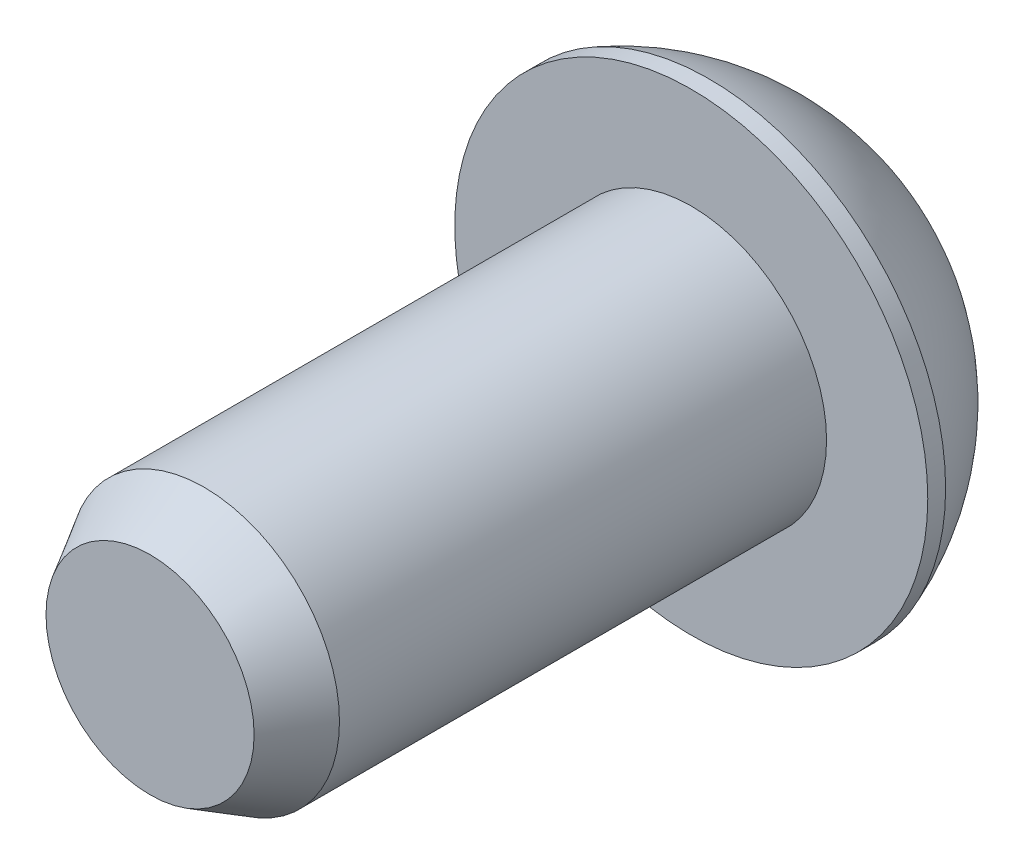
SolidWorks part; units mm, degrees
ref_plane "Front Plane" through (0, 0, 0) normal (0, 0, 1) x (1, 0, 0)
ref_plane "Top Plane" through (0, 0, 0) normal (0, 1, 0) x (1, 0, 0)
ref_plane "Right Plane" through (0, 0, 0) normal (1, 0, 0) x (0, 0, -1)
sketch "Sketch1" plane through (0, 0, 0) normal (0, 1, 0) x (1, 0, 0)
  line L0 (5.5499, -3.3528) -> (5.5499, -2.9337)
  line L1 (5.5499, -3.3528) -> (0, -3.3528)
  line L2 (0, 0) -> (3.175, 0)
  line L3 (0, 0) -> (0, 0.8046) construction
  line L4 (0, -3.3528) -> (0, 0)
  arc A0 (5.5499, -2.9337) -> (3.175, 0) centre (0, -4.9984) ccw
revolve "Revolve1" add sketch "Sketch1" angle 360 about L3
sketch "Sketch2" plane through (0, 0, 0) normal (0, 0, -1) x (-1, 0, 0)
  line L1 (2.2914, 0) -> (1.1457, 1.9844)
  line L2 (1.1457, 1.9844) -> (-1.1457, 1.9844)
  line L3 (-1.1457, 1.9844) -> (-2.2914, 0)
  line L4 (-2.2914, 0) -> (-1.1457, -1.9844)
  line L5 (-1.1457, -1.9844) -> (1.1457, -1.9844)
  line L6 (1.1457, -1.9844) -> (2.2914, 0)
  circle A0 centre (0, 0) radius 1.9844 construction
extrude "Cut-Extrude1" cut sketch "Sketch2" against normal blind 2.2225
sketch "Sketch3" plane through (0, 0, 3.3528) normal (0, 0, 1) x (1, 0, 0)
  circle A0 centre (0, 0) radius 3.175
  dimension "D1" = 6.35
extrude "Boss-Extrude1" add sketch "Sketch3" along normal blind 12.7
chamfer "Chamfer1" distance 1.27 angle 30 1 edges at (3.175, 0, 16.0528)
